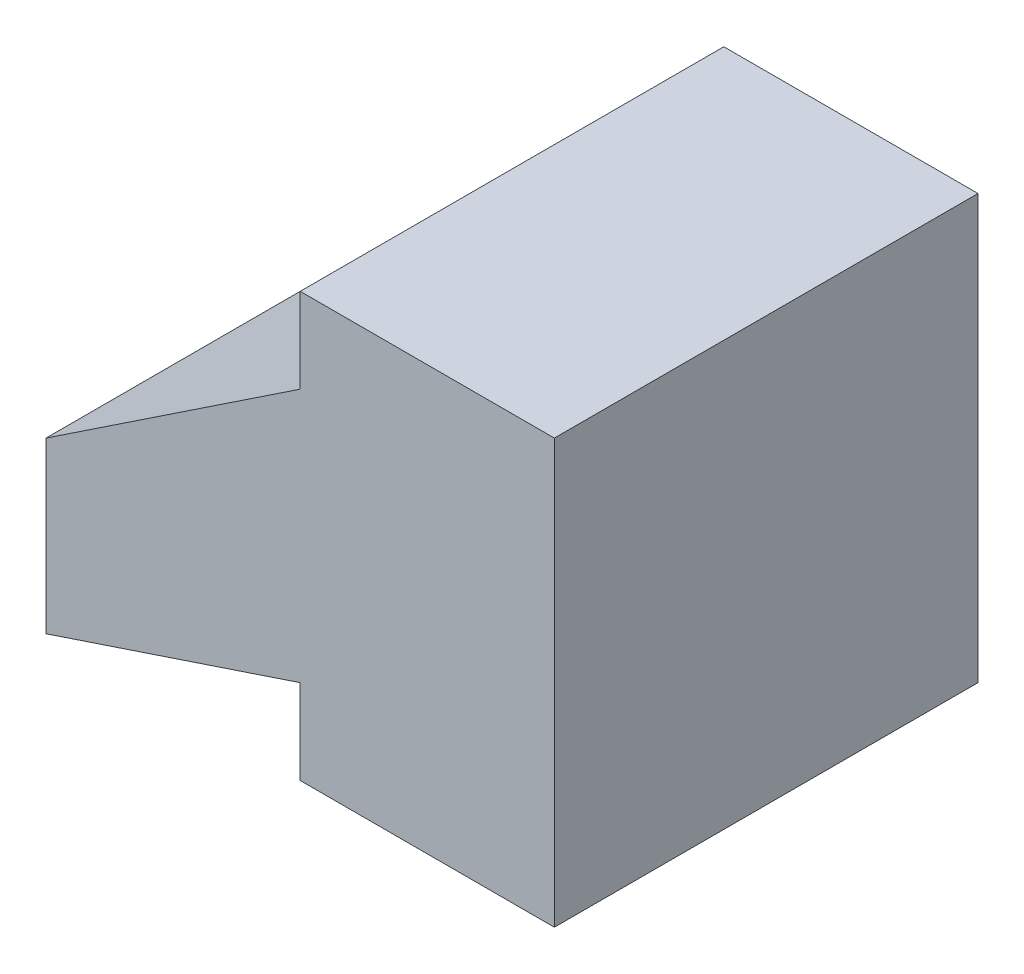
SolidWorks part; units mm, degrees
ref_plane "Front Plane" through (0, 0, 0) normal (0, 0, 1) x (1, 0, 0)
ref_plane "Top Plane" through (0, 0, 0) normal (0, 1, 0) x (1, 0, 0)
ref_plane "Right Plane" through (0, 0, 0) normal (1, 0, 0) x (0, 0, -1)
sketch "Sketch1" plane through (0, 0, 0) normal (0, 0, 1) x (1, 0, 0)
  line L0 (0, 0) -> (0, 1)
  line L1 (0, 1) -> (-3, 0)
  line L2 (-3, 0) -> (-3, 2)
  line L3 (-3, 2) -> (0, 4)
  line L4 (0, 4) -> (0, 5)
  line L5 (0, 5) -> (3, 5)
  line L6 (3, 5) -> (3, 0)
  line L7 (3, 0) -> (0, 0)
  dimension "D1" = 1
  dimension "D2" = 2
  dimension "D3" = 1
  dimension "D4" = 2
  dimension "D5" = 5
  dimension "D6" = 3
  dimension "D7" = 3
extrude "Boss-Extrude1" add sketch "Sketch1" along normal blind 5
